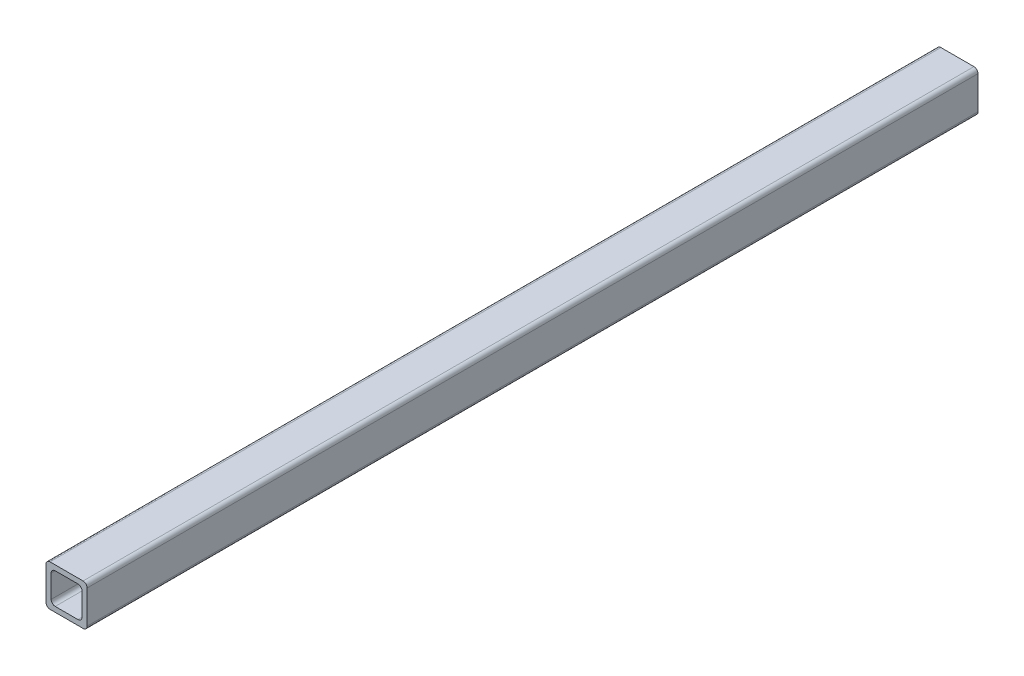
SolidWorks part; units mm, degrees
ref_plane "Alzado" through (0, 0, 0) normal (0, 0, 1) x (1, 0, 0)
ref_plane "Planta" through (0, 0, 0) normal (0, 1, 0) x (1, 0, 0)
ref_plane "Vista lateral" through (0, 0, 0) normal (1, 0, 0) x (0, 0, -1)
sketch "Croquis1" plane through (0, 0, 0) normal (0, 0, 1) x (1, 0, 0)
  line L1 (-7.025, -9.525) -> (7.025, -9.525)
  line L2 (-9.525, -7.025) -> (-9.525, 7.025)
  line L3 (-7.025, 9.525) -> (7.025, 9.525)
  line L4 (9.525, -7.025) -> (9.525, 7.025)
  line L5 (-9.525, -9.525) -> (9.525, 9.525) construction
  line L6 (-9.525, 9.525) -> (9.525, -9.525) construction
  line L7 (-10.2, -12.7) -> (10.2, -12.7)
  line L8 (-12.7, -10.2) -> (-12.7, 10.2)
  line L9 (-10.2, 12.7) -> (10.2, 12.7)
  line L10 (12.7, -10.2) -> (12.7, 10.2)
  line L11 (-12.7, -12.7) -> (12.7, 12.7) construction
  line L12 (-12.7, 12.7) -> (12.7, -12.7) construction
  arc A0 (-7.025, -9.525) -> (-9.525, -7.025) centre (-7.025, -7.025) cw
  arc A1 (7.025, -9.525) -> (9.525, -7.025) centre (7.025, -7.025) ccw
  arc A2 (9.525, 7.025) -> (7.025, 9.525) centre (7.025, 7.025) ccw
  arc A3 (12.7, -10.2) -> (10.2, -12.7) centre (10.2, -10.2) cw
  arc A4 (-10.2, -12.7) -> (-12.7, -10.2) centre (-10.2, -10.2) cw
  arc A5 (12.7, 10.2) -> (10.2, 12.7) centre (10.2, 10.2) ccw
  arc A6 (-9.525, 7.025) -> (-7.025, 9.525) centre (-7.025, 7.025) cw
  arc A7 (-10.2, 12.7) -> (-12.7, 10.2) centre (-10.2, 10.2) ccw
  point P0 (0, 0)
  point P6 (0, 0)
  dimension "D3" = 2.5
  dimension "D1" = 25.4
  dimension "D2" = 3.175
extrude "Saliente-Extruir1" add sketch "Croquis1" along normal blind 550
